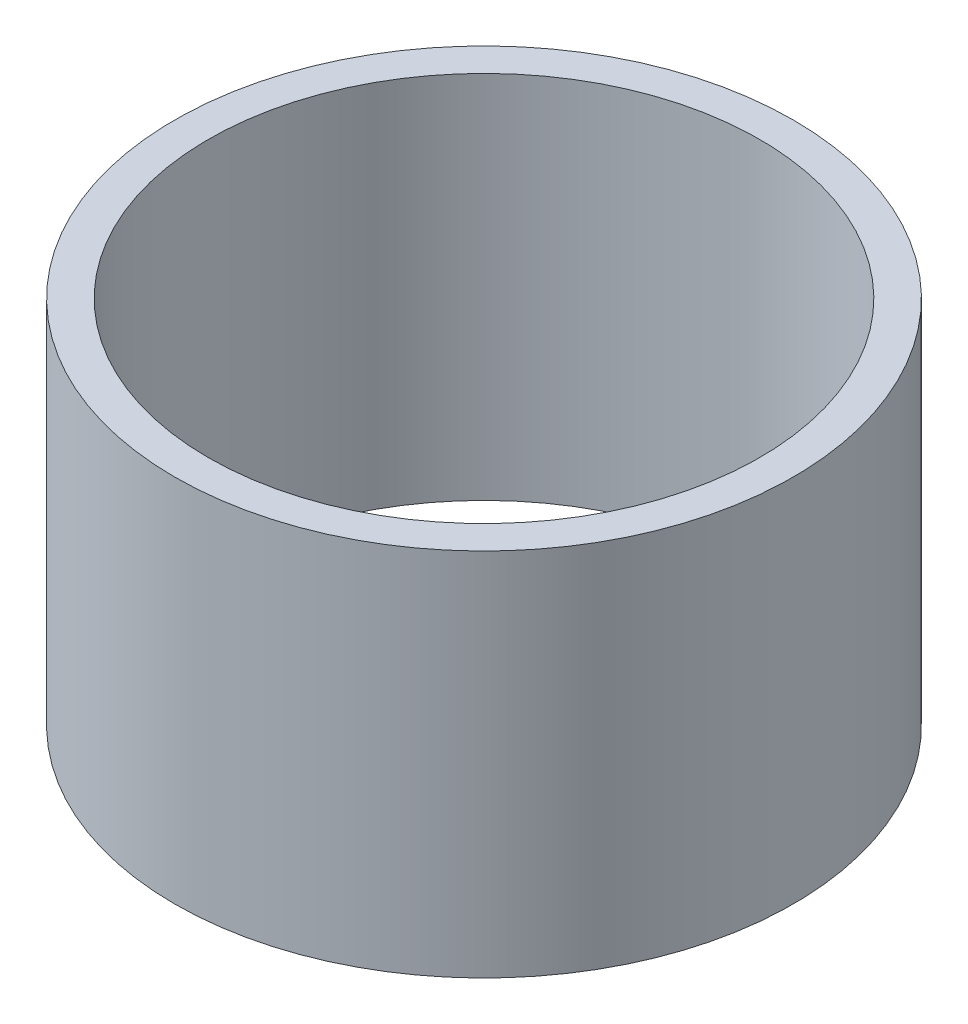
SolidWorks part; units mm, degrees
ref_plane "前视基准面" through (0, 0, 0) normal (0, 0, 1) x (1, 0, 0)
ref_plane "上视基准面" through (0, 0, 0) normal (0, 1, 0) x (1, 0, 0)
ref_plane "右视基准面" through (0, 0, 0) normal (1, 0, 0) x (0, 0, -1)
other "Configuration Table"
sketch "草图1" plane through (0, 0, 0) normal (0, 1, 0) x (1, 0, 0)
  circle A0 centre (0, 0) radius 20.5
  circle A1 centre (0, 0) radius 23
extrude "凸台-拉伸1" add sketch "草图1" along normal blind 27.5
